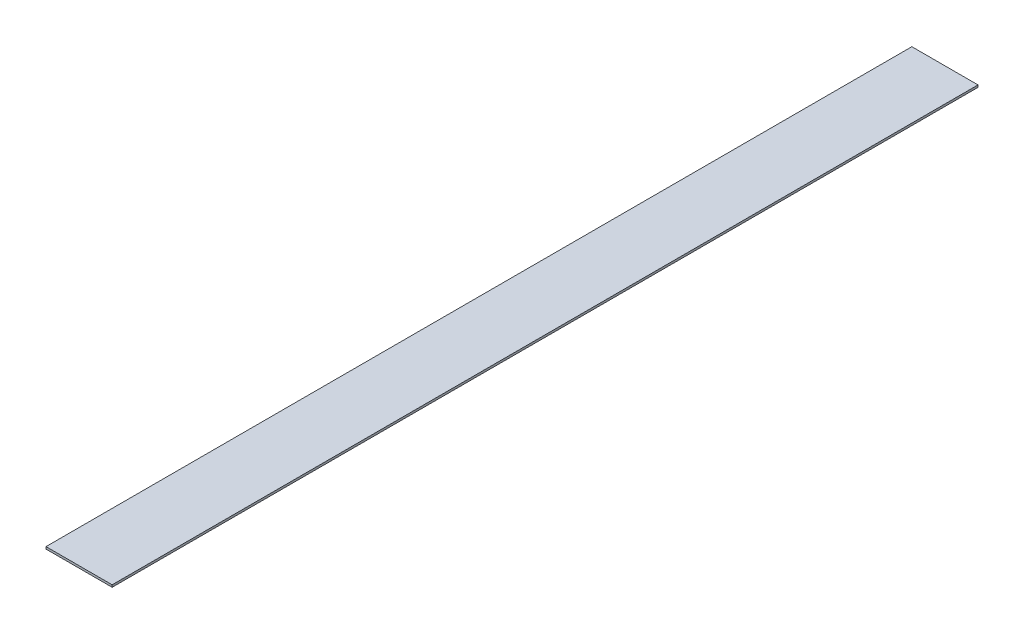
SolidWorks part; units mm, degrees
material "PMMA"
ref_plane "Front Plane" through (0, 0, 0) normal (0, 0, 1) x (1, 0, 0)
ref_plane "Top Plane" through (0, 0, 0) normal (0, 1, 0) x (1, 0, 0)
ref_plane "Right Plane" through (0, 0, 0) normal (1, 0, 0) x (0, 0, -1)
sketch "Sketch1" plane through (0, 0, 0) normal (0, 0, 1) x (1, 0, 0)
  line L1 (-23.114, -0.762) -> (23.114, -0.762)
  line L2 (-23.114, -0.762) -> (-23.114, 0.762)
  line L3 (-23.114, 0.762) -> (23.114, 0.762)
  line L4 (23.114, -0.762) -> (23.114, 0.762)
  line L5 (-23.114, -0.762) -> (23.114, 0.762) construction
  line L6 (-23.114, 0.762) -> (23.114, -0.762) construction
  point P0 (0, 0)
  dimension "D1" = 46.228
  dimension "D2" = 1.524
extrude "Diffuser Profile" add sketch "Sketch1" along normal mid plane 605.028
